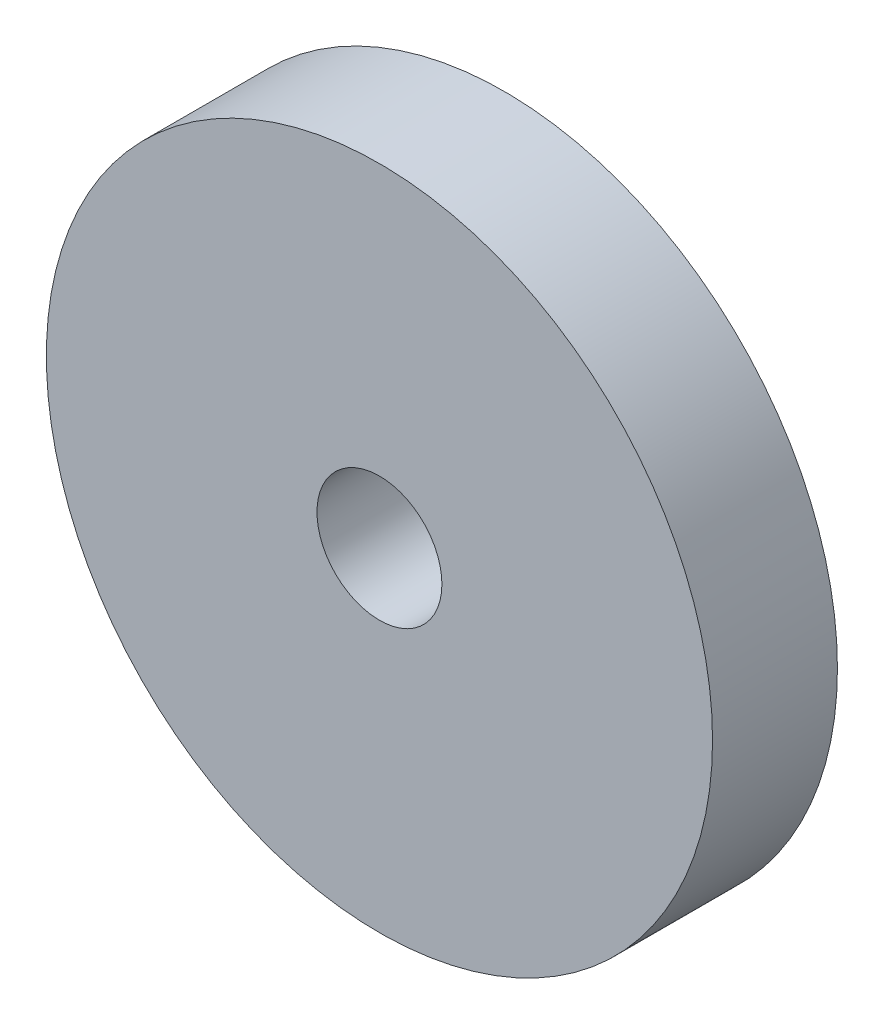
SolidWorks part; units mm, degrees
ref_plane "Front Plane" through (0, 0, 0) normal (0, 0, 1) x (1, 0, 0)
ref_plane "Top Plane" through (0, 0, 0) normal (0, 1, 0) x (1, 0, 0)
ref_plane "Right Plane" through (0, 0, 0) normal (1, 0, 0) x (0, 0, -1)
sketch "Sketch1" plane through (0, 0, 0) normal (0, 0, 1) x (1, 0, 0)
  circle A0 centre (0, 0) radius 9.525
  circle A1 centre (0, 0) radius 50.8
  dimension "D1" = 101.6
  dimension "D2" = 19.05
extrude "Boss-Extrude1" add sketch "Sketch1" along normal blind 19.05
